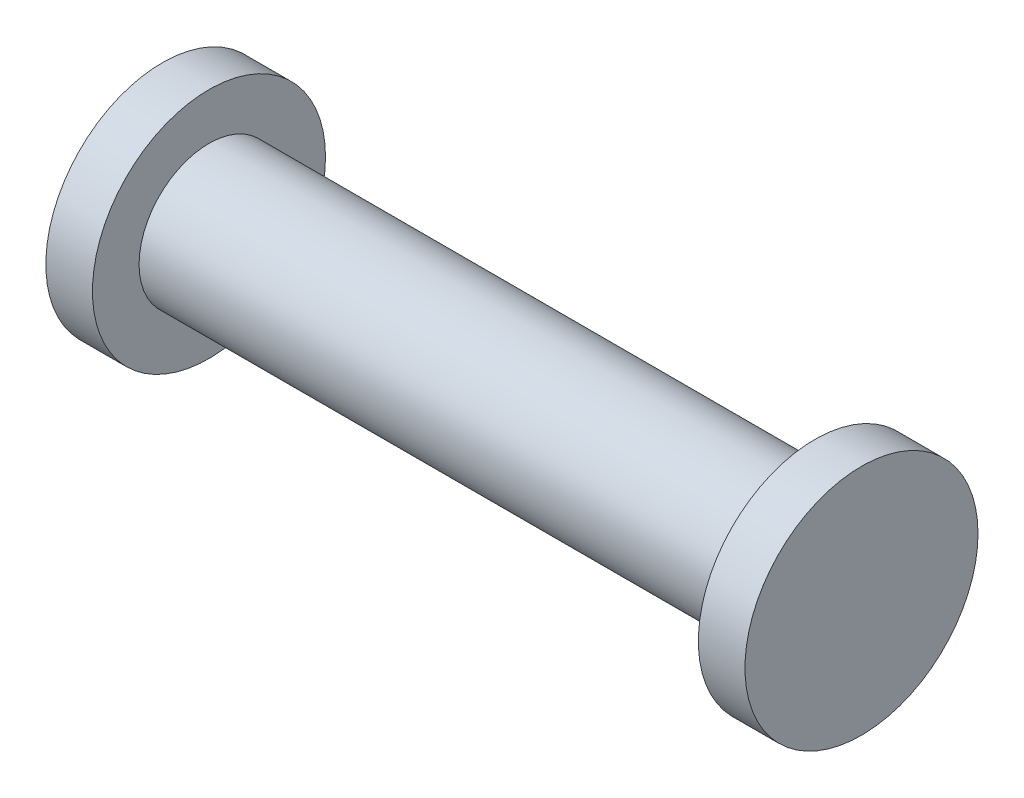
SolidWorks part; units mm, degrees
ref_plane "Front Plane" through (0, 0, 0) normal (0, 0, 1) x (1, 0, 0)
ref_plane "Top Plane" through (0, 0, 0) normal (0, 1, 0) x (1, 0, 0)
ref_plane "Right Plane" through (0, 0, 0) normal (1, 0, 0) x (0, 0, -1)
sketch "Sketch1" plane through (0, 0, 0) normal (1, 0, 0) x (0, 0, -1)
  circle A0 centre (0, 0) radius 7.5
  dimension "D1" = 15
extrude "Boss-Extrude1" add sketch "Sketch1" along normal mid plane 65
sketch "Sketch4" plane through (32.5, 0, 0) normal (1, 0, 0) x (0, 0, -1)
  circle A0 centre (0, 0) radius 12.5
  dimension "D1" = 25
extrude "Boss-Extrude3" add sketch "Sketch4" along normal blind 5
mirror "Mirror1" about plane through (0, 0, 0) normal (1, 0, 0) of "Boss-Extrude3"
